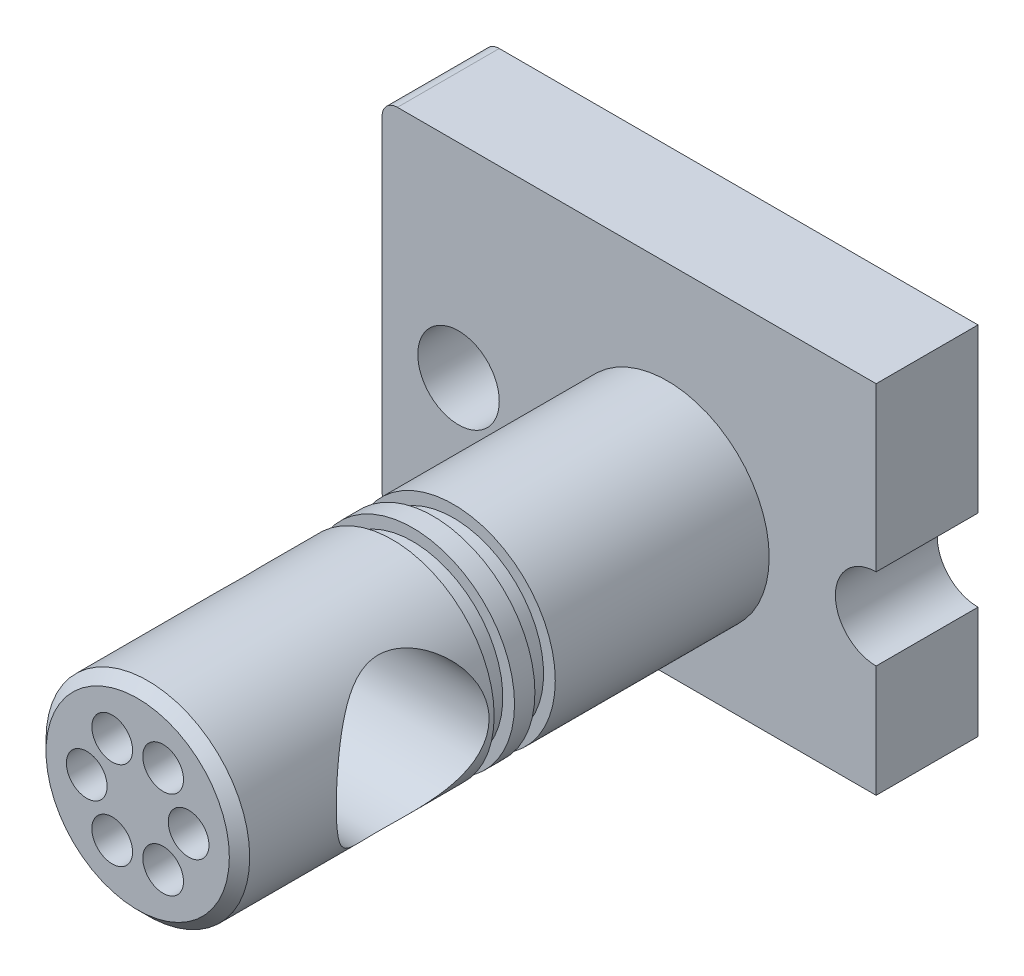
SolidWorks part; units mm, degrees
ref_plane "Front Plane" through (0, 0, 0) normal (0, 0, 1) x (1, 0, 0)
ref_plane "Top Plane" through (0, 0, 0) normal (0, 1, 0) x (1, 0, 0)
ref_plane "Right Plane" through (0, 0, 0) normal (1, 0, 0) x (0, 0, -1)
sketch "Sketch1" plane through (0, 0, 0) normal (0, 0, 1) x (1, 0, 0)
  line L0 (41, -8) -> (41, -30)
  line L1 (41, 40) -> (-56, 40)
  line L2 (41, 40) -> (41, 8)
  line L3 (41, -30) -> (-56, -30)
  line L4 (-56, 40) -> (-56, -30)
  circle A0 centre (-41, 0) radius 8
  arc A1 (41, 8) -> (41, -8) centre (41, 0) ccw
  point P9 (0, 0)
  dimension "D5" = 16
  dimension "D1" = 70
  dimension "D2" = 97
  dimension "D3" = 30
  dimension "D4" = 56
  dimension "D6" = 15
extrude "Boss-Extrude1" add sketch "Sketch1" along normal blind 20
sketch "Sketch2" plane through (0, 0, 20) normal (0, 0, 1) x (1, 0, 0)
  circle A0 centre (0, 0) radius 20
  dimension "D1" = 40
extrude "Boss-Extrude2" add sketch "Sketch2" along normal blind 104
sketch "Sketch3" plane through (0, 0, 0) normal (1, 0, 0) x (0, 0, -1)
  circle A0 centre (-90, 0) radius 15
  dimension "D1" = 30
  dimension "D2" = 90
extrude "Cut-Extrude1" cut sketch "Sketch3" against normal through all both and the other way through all
sketch "Sketch4" plane through (0, 0, 0) normal (1, 0, 0) x (0, 0, -1)
  line L0 (-20, 20) -> (-124, 20) construction
  line L1 (-74, 20) -> (-70, 20)
  line L2 (-74, 20) -> (-74, 17.7)
  line L3 (-74, 17.7) -> (-70, 17.7)
  line L4 (-70, 20) -> (-70, 17.7)
  line L5 (-20, 8) -> (-20, 40) construction
  line L6 (-66, 20) -> (-62, 20)
  line L7 (-66, 20) -> (-66, 17.7)
  line L8 (-66, 17.7) -> (-62, 17.7)
  line L9 (-62, 20) -> (-62, 17.7)
  line L10 (0, 0) -> (-133.7463, 0) construction
  dimension "D1" = 4
  dimension "D2" = 4
  dimension "D3" = 4
  dimension "D4" = 2.3
  dimension "D5" = 42
revolve "Cut-Revolve1" cut sketch "Sketch4" angle 360 about L10
sketch "Sketch5" plane through (0, 0, 124) normal (0, 0, 1) x (1, 0, 0)
  circle A0 centre (0, 0) radius 10 construction
  circle A1 centre (10, 0) radius 4
  dimension "D1" = 20
  dimension "D2" = 8
extrude "Cut-Extrude2" cut sketch "Sketch5" against normal blind 30
pattern_circular "CirPattern1" count 6 over 360 about axis through (0, 0, 0) along (0, 0, 1) of "Cut-Extrude2"
fillet "Fillet1" radius 3 2 edges at (-56, -30, 10) (-56, 40, 10)
chamfer "Chamfer1" distance 2 1 edges at (20, 0, 124)
